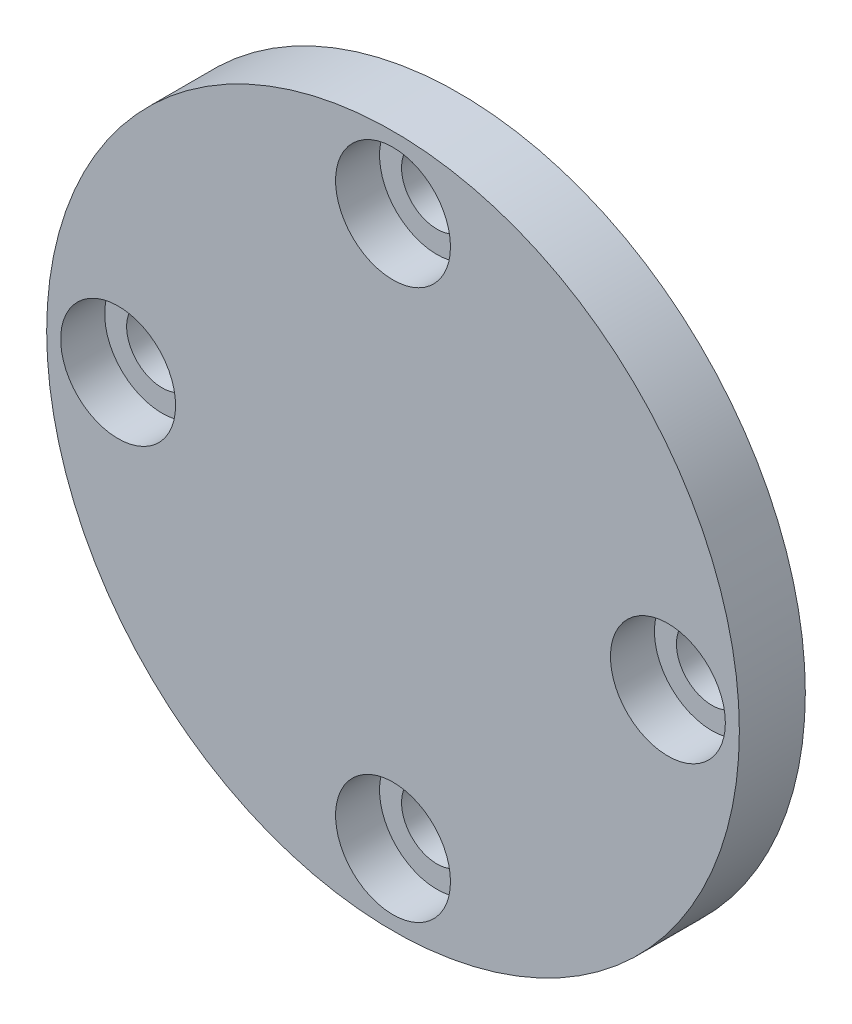
SolidWorks part; units mm, degrees
material "ABS"
ref_plane "Front Plane" through (0, 0, 0) normal (0, 0, 1) x (1, 0, 0)
ref_plane "Top Plane" through (0, 0, 0) normal (0, 1, 0) x (1, 0, 0)
ref_plane "Right Plane" through (0, 0, 0) normal (1, 0, 0) x (0, 0, -1)
sketch "Sketch1" plane through (0, 0, 0) normal (0, 0, 1) x (1, 0, 0)
  line L0 (-31.5, 0) -> (31.5, 0) construction
  line L1 (0, 31.5) -> (0, -31.5) construction
  circle A0 centre (0, 0) radius 31.5
  circle A6 centre (0, -25) radius 3.225
  circle A7 centre (-25, 0) radius 3.225
  circle A8 centre (0, 25) radius 3.225
  circle A9 centre (25, 0) radius 3.225
  point P28 (0, 0)
  dimension "D1" = 63
  dimension "D7" = 6.45
  dimension "D6" = 25
  dimension "D8" = 4
extrude "Main PA10 Flange" add sketch "Sketch1" along normal blind 6
sketch "Sketch3" plane through (0, 0, 6) normal (0, 0, 1) x (1, 0, 0)
  circle A0 centre (0, -25) radius 5.225
  circle A1 centre (-25, 0) radius 5.225
  circle A2 centre (0, 25) radius 5.225
  circle A3 centre (25, 0) radius 5.225
  point P12 (0, 0)
  dimension "D1" = 10.45
  dimension "D2" = 4
extrude "M6 Hole" cut sketch "Sketch3" against normal blind 4
sketch "Coupling Base" plane through (0, 0, 6) normal (0, 0, 1) x (1, 0, 0)
  line L1 (-8.5, -19) -> (8.5, -19)
  line L2 (-8.5, -19) -> (-8.5, 19)
  line L3 (-8.5, 19) -> (8.5, 19)
  line L4 (8.5, -19) -> (8.5, 19)
  line L5 (-8.5, -19) -> (8.5, 19) construction
  line L6 (-8.5, 19) -> (8.5, -19) construction
  point P0 (0, 0)
  dimension "D1" = 17
  dimension "D2" = 38
equation "\"D7@Sketch1\"  = 6 + \"print_free@Parameters@FabricationParameters.SLDPRT\""
equation "\"D1@Sketch3\" = 10 + \"print_free@Parameters@FabricationParameters.SLDPRT\""
equation "\"D1@M6 Hole\"=4.00mm"
